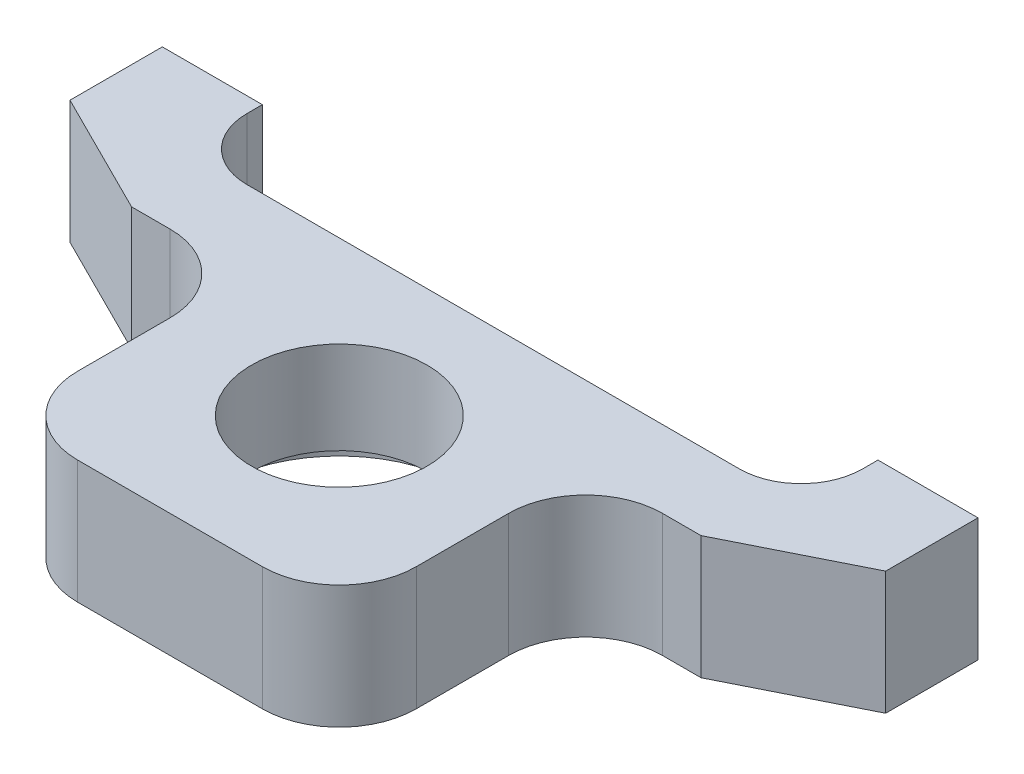
SolidWorks part; units mm, degrees
ref_plane "Front Plane" through (0, 0, 0) normal (0, 0, 1) x (1, 0, 0)
ref_plane "Top Plane" through (0, 0, 0) normal (0, 1, 0) x (1, 0, 0)
ref_plane "Right Plane" through (0, 0, 0) normal (1, 0, 0) x (0, 0, -1)
ref_plane "Plane1" through (0, 0, 0) normal (0, -1, 0) x (1, 0, 0)
sketch "Sketch1" plane through (0, 0, 0) normal (0, -1, 0) x (1, 0, 0)
  line L0 (26.5, 0) -> (26.5, 26)
  line L1 (26.5, 26) -> (-26.5, 26)
  line L2 (-26.5, 26) -> (-26.5, 0)
  line L3 (-26.5, 0) -> (26.5, 0)
extrude "Boss-Extrude1" add sketch "Sketch1" against normal blind 8
sketch "Sketch2" plane through (0, 8, 0) normal (0, 1, 0) x (-1, 0, 0)
  line L0 (-11, 10) -> (-11, 26)
  line L1 (-11, 26) -> (-26.5, 26)
  line L2 (-26.5, 26) -> (-26.5, 10)
  line L3 (-26.5, 10) -> (-11, 10)
extrude "Cut-Extrude1" cut sketch "Sketch2" against normal through all
sketch "Sketch3" plane through (0, 8, 0) normal (0, 1, 0) x (-1, 0, 0)
  line L0 (11, 26) -> (11, 10)
  line L1 (11, 10) -> (26.5, 10)
  line L2 (26.5, 10) -> (26.5, 26)
  line L3 (26.5, 26) -> (11, 26)
extrude "Cut-Extrude2" cut sketch "Sketch3" against normal through all
sketch "Sketch4" plane through (0, 8, 0) normal (0, 1, 0) x (-1, 0, 0)
  line L0 (20, 0) -> (20, 5)
  line L1 (20, 5) -> (-20, 5)
  line L2 (-20, 5) -> (-20, 0)
  line L3 (-20, 0) -> (20, 0)
extrude "Cut-Extrude3" cut sketch "Sketch4" against normal through all
hole_wizard "CBORE for M10 Hex Head Bolt1" positions "Sketch6" profile "Sketch5" counterbore size "M10" standard "ANSI Metric" end condition through all
sketch "Sketch6" plane through (0, 0, 0) normal (0, -1, 0) x (-1, 0, 0)
  point P0 (0, -15)
sketch "Sketch5" plane through (0, 0, 15) normal (1, 0, 0) x (0, 0, -1)
  line L0 (0, 0) -> (0, 8)
  line L1 (0, 8) -> (5.7, 8)
  line L3 (5.7, 8) -> (5.7, 2)
  line L4 (5.7, 2) -> (8.1, 2)
  line L5 (8.1, 2) -> (8.1, 0)
  line L7 (8.1, 0) -> (0, 0)
  line L11 (0, -6.35) -> (0, 107.95) construction
  dimension "Thru Hole Dia." = 11.4
  dimension "Thru Hole Depth" = 8
  dimension "C'Bore Dia." = 16.2
  dimension "C'Bore Depth" = 2
hole_wizard "Ø3.3 (3.3) Diameter Hole1" positions "Sketch8" profile "Sketch7" hole size "Ø3.3" standard "ANSI Metric"
sketch "Sketch8" plane through (0, 0, 0) normal (0, 0, -1) x (-1, 0, 0)
  point P0 (-23.25, 4)
  point P1 (23.25, 4)
sketch "Sketch7" plane through (23.25, 4, 0) normal (1, 0, 0) x (0, 1, 0)
  line L0 (0, 0) -> (0, 6.9914)
  line L1 (0, 6.9914) -> (1.65, 6)
  line L2 (1.65, 6) -> (1.65, 0)
  line L5 (1.65, 0) -> (0, 0)
  line L10 (0, 6.9914) -> (-1.65, 6) construction
  line L11 (0, -6.35) -> (0, 107.95) construction
  dimension "Hole Dia." = 3.3
  dimension "Hole Depth" = 6
  dimension "Drill Angle" = 118
fillet "Fillet1" radius 4 2 edges at (-20, 4, 5) (20, 4, 5)
fillet "Fillet2" radius 5 4 edges at (11, 4, 10) (11, 4, 26) (-11, 4, 26) (-11, 4, 10)
chamfer "Chamfer1" distance 8 distance2 4 1 edges at (-26.5, 4, 10)
chamfer "Chamfer2" distance 4 distance2 8 1 edges at (26.5, 4, 10)
